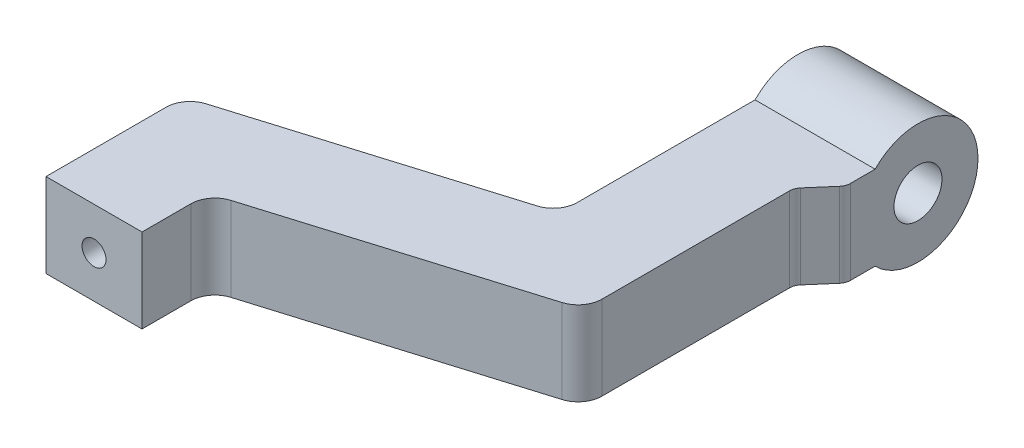
SolidWorks part; units mm, degrees
material "6061 Alloy"
ref_plane "Front Plane" through (0, 0, 0) normal (0, 0, 1) x (1, 0, 0)
ref_plane "Top Plane" through (0, 0, 0) normal (0, 1, 0) x (1, 0, 0)
ref_plane "Right Plane" through (0, 0, 0) normal (1, 0, 0) x (0, 0, -1)
sketch "Sketch2" plane through (0, 0, 0) normal (0, 1, 0) x (1, 0, 0)
  line L0 (-1.5007, 12.1284) -> (2.4993, 12.1284)
  line L1 (15.4993, 31.4445) -> (15.4993, 28.4445)
  line L3 (-1.5007, 12.1284) -> (2.4993, 12.1284)
  line L4 (-1.5007, 12.1284) -> (-1.5007, 17.1284)
  line L6 (2.4993, 12.1284) -> (2.4993, 14.1622)
  line L8 (3.2089, 15.1191) -> (13.7898, 18.3304)
  line L9 (14.4993, 19.2873) -> (14.4993, 27.2873)
  line L10 (-0.7911, 18.0853) -> (9.7898, 21.2966)
  line L11 (10.4993, 22.2535) -> (10.4993, 26.2101)
  line L13 (10.4993, 31.4445) -> (15.4993, 31.4445)
  line L15 (10.4993, 26.2101) -> (10.4993, 31.4445)
  line L16 (15.4993, 28.4445) -> (14.4993, 27.2873)
  line L18 (15.4993, 31.4445) -> (15.4993, 28.8783)
  arc A0 (3.2089, 15.1191) -> (2.4993, 14.1622) centre (3.4993, 14.1622) ccw
  arc A1 (-1.5007, 17.1284) -> (-0.7911, 18.0853) centre (-0.5007, 17.1284) cw
  arc A2 (13.7898, 18.3304) -> (14.4993, 19.2873) centre (13.4993, 19.2873) ccw
  arc A3 (9.7898, 21.2966) -> (10.4993, 22.2535) centre (9.4993, 22.2535) ccw
  point P3 (0.4993, 12.1284)
  point P17 (7.6961, 22.7887)
  dimension "D2" = 1
  dimension "D1" = 4
  dimension "D3" = 15
  dimension "D4" = 4
  dimension "D5" = 4
  dimension "D7" = 8
  dimension "D8" = 5
  dimension "D9" = 3
extrude "Boss-Extrude2" add sketch "Sketch2" along normal blind 3.5
sketch "Sketch3" plane through (10.4993, 0, 0) normal (-1, 0, 0) x (0, 0, 1)
  line L2 (-31.4445, 0) -> (-31.4445, 3.5) construction
  circle A3 centre (-31.4445, 1.75) radius 2.5
extrude "Boss-Extrude3" add sketch "Sketch3" against normal blind 5
fillet "Fillet2" radius 0.5 2 edges at (14.4993, 1.75, -27.2873) (15.4993, 1.75, -28.4445)
sketch "Sketch5" plane through (0, 0, -12.1284) normal (0, 0, 1) x (1, 0, 0)
  line L0 (-1.5007, 3.5) -> (2.4993, 3.5) construction
  line L1 (-1.5007, 0) -> (-1.5007, 3.5) construction
  circle A0 centre (0.4993, 1.75) radius 0.5
  dimension "D1" = 1.75
  dimension "D2" = 2
extrude "Cut-Extrude1" cut sketch "Sketch5" against normal blind 1
sketch "Sketch6" plane through (10.4993, 0, 0) normal (-1, 0, 0) x (0, 0, 1)
  circle A0 centre (-31.4445, 1.75) radius 1
  dimension "D1" = 2
extrude "Cut-Extrude2" cut sketch "Sketch6" against normal through all
